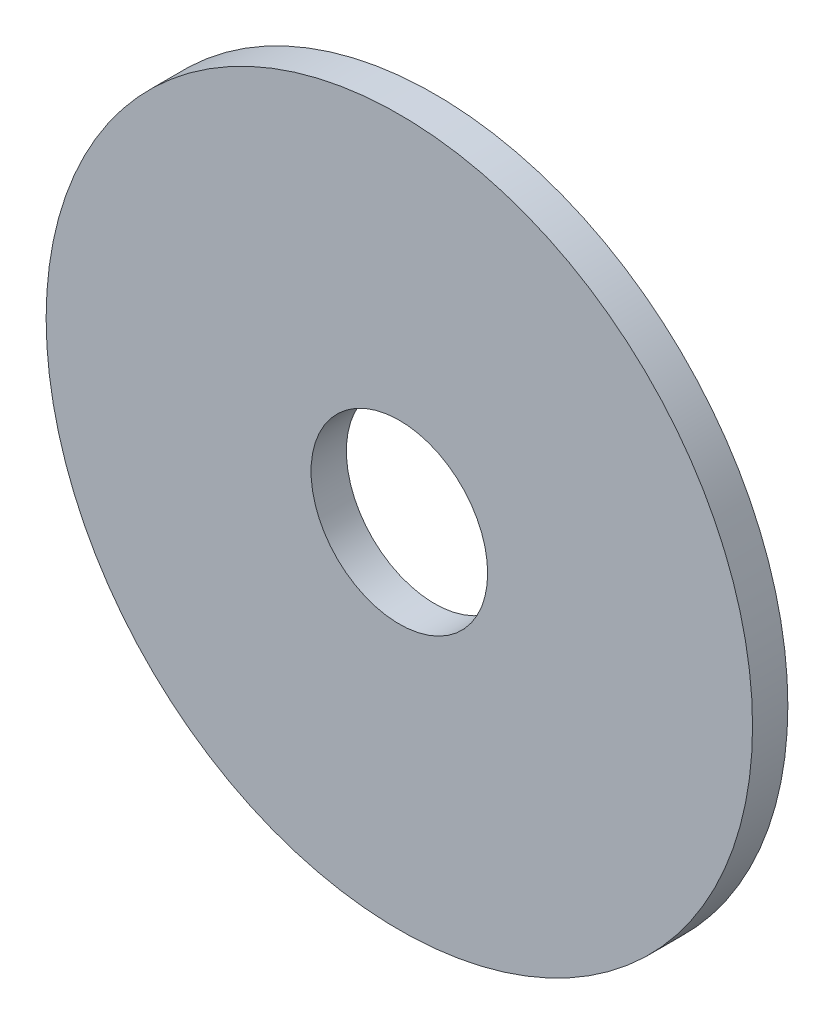
SolidWorks part; units mm, degrees
ref_plane "Front Plane" through (0, 0, 0) normal (0, 0, 1) x (1, 0, 0)
ref_plane "Top Plane" through (0, 0, 0) normal (0, 1, 0) x (1, 0, 0)
ref_plane "Right Plane" through (0, 0, 0) normal (1, 0, 0) x (0, 0, -1)
sketch "Sketch1" plane through (0, 0, 0) normal (0, 0, 1) x (1, 0, 0)
  circle A0 centre (0, 0) radius 20
extrude "Boss-Extrude1" add sketch "Sketch1" along normal blind 2
sketch "Sketch2" plane through (0, 0, 2) normal (0, 0, 1) x (1, 0, 0)
  circle A0 centre (0, 0) radius 5
extrude "Cut-Extrude1" cut sketch "Sketch2" against normal blind 4
